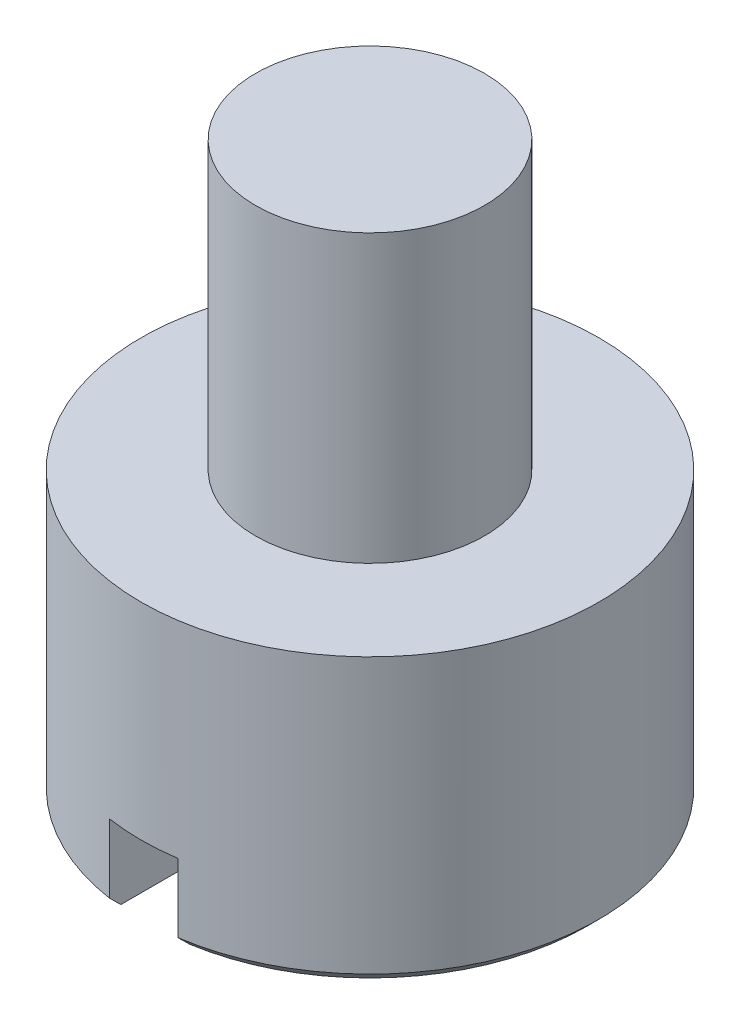
SolidWorks part; units mm, degrees
ref_plane "Front Plane" through (0, 0, 0) normal (0, 0, 1) x (1, 0, 0)
ref_plane "Top Plane" through (0, 0, 0) normal (0, 1, 0) x (1, 0, 0)
ref_plane "Right Plane" through (0, 0, 0) normal (1, 0, 0) x (0, 0, -1)
sketch "Sketch2" plane through (0, 0, 0) normal (0, 1, 0) x (1, 0, 0)
  circle A0 centre (0, 0) radius 1
  dimension "d1" = 2
extrude "Boss-Extrude1" add sketch "Sketch2" along normal blind 1.25
sketch "Sketch3" plane through (0, 1.25, 0) normal (0, 1, 0) x (1, 0, 0)
  circle A0 centre (0, 0) radius 0.5
  dimension "d2" = 1
extrude "Boss-Extrude2" add sketch "Sketch3" along normal blind 1.25
chamfer "Chamfer1" distance 0.05 angle 45 1 edges at (0, 0, 1)
sketch "Sketch4" plane through (0, 0, 0) normal (0, 0, 1) x (1, 0, 0)
  line L1 (-0.15, 0.35) -> (0.15, 0.35)
  line L2 (-0.15, 0.35) -> (-0.15, 0)
  line L3 (-0.15, 0) -> (0.15, 0)
  line L4 (0.15, 0.35) -> (0.15, 0)
  dimension "D1" = 0.3
  dimension "D2" = 0.35
extrude "Cut-Extrude1" cut sketch "Sketch4" against normal through all both and the other way through all
